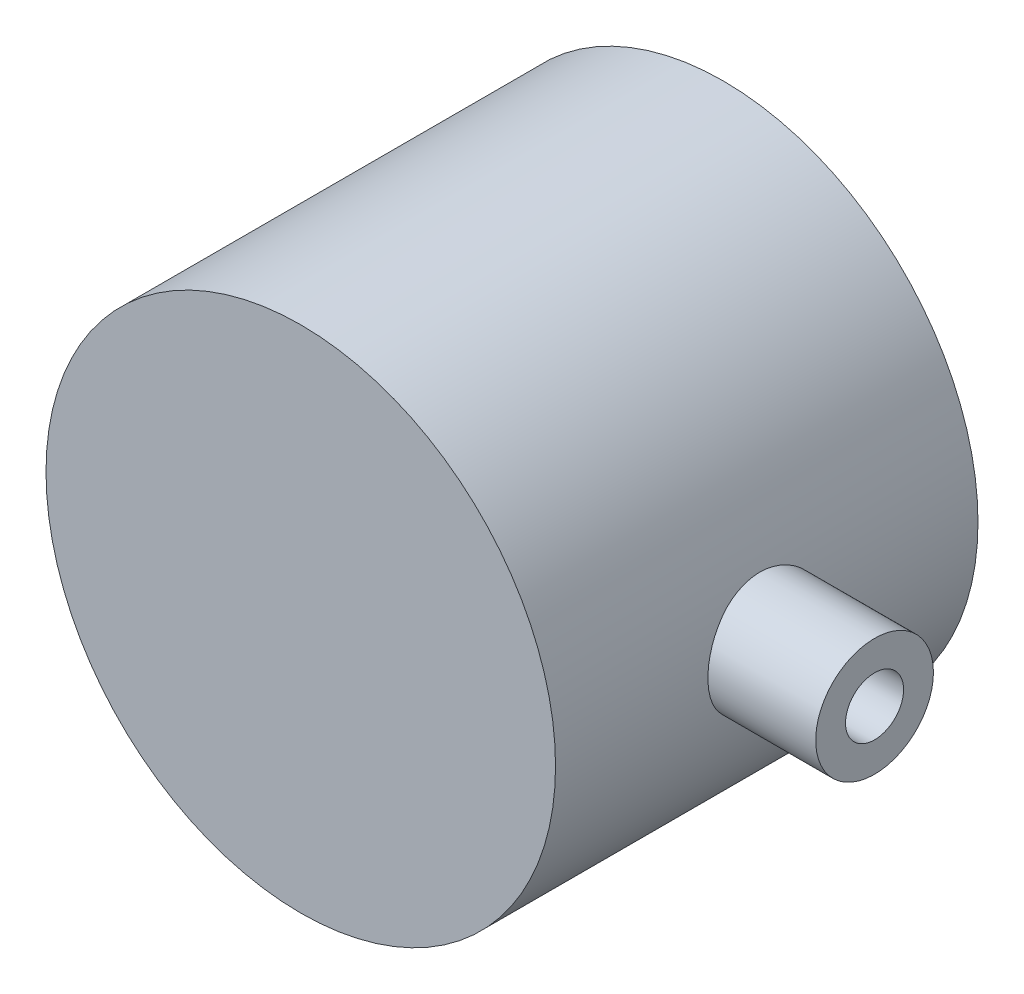
SolidWorks part; units mm, degrees
ref_plane "Ebene vorne" through (0, 0, 0) normal (0, 0, 1) x (1, 0, 0)
ref_plane "Ebene oben" through (0, 0, 0) normal (0, 1, 0) x (1, 0, 0)
ref_plane "Ebene rechts" through (0, 0, 0) normal (1, 0, 0) x (0, 0, -1)
sketch "Sketch1" plane through (0, 0, 0) normal (0, 0, 1) x (1, 0, 0)
  circle A1 centre (0, 0) radius 24.123
  dimension "D3" = 48.246
extrude "Boss-Extrude1" add sketch "Sketch1" along normal blind 35 and the other way blind 5
sketch "Sketch2" plane through (0, 0, 0) normal (1, 0, 0) x (0, 0, -1)
  line L0 (0, 24.123) -> (0, -24.123) construction
  circle A0 centre (-15, 0) radius 3.25
  dimension "D1" = 15
  dimension "D2" = 6.5
extrude "Cut-Extrude2" cut sketch "Sketch2" along normal blind 19.25
sketch "Sketch4" plane through (0, 0, 0) normal (0, 1, 0) x (1, 0, 0)
  line L0 (0, -18.25) -> (0, -11.75) construction
  line L1 (-24.123, 0) -> (24.123, 0) construction
  circle A0 centre (0, -15) radius 2.75
  dimension "D1" = 15
  dimension "D2" = 5.5
extrude "Cut-Extrude3" cut sketch "Sketch4" against normal blind 200
sketch "Sketch6" plane through (0, 0, 0) normal (0, 1, 0) x (1, 0, 0)
  line L0 (0, -18.25) -> (0, -11.75) construction
  line L1 (-24.123, -35) -> (24.123, -35) construction
  circle A0 centre (0, -15) radius 5.25
  dimension "D1" = 20
  dimension "D2" = 10.5
extrude "Cut-Extrude9" cut sketch "Sketch6" along normal blind 4.533 from offset 24.123 offset against normal yes
sketch "Sketch7" plane through (0, 0, -5) normal (0, 0, -1) x (-1, 0, 0)
  circle A0 centre (0, 0) radius 17.25
  dimension "D1" = 34.5
extrude "Cut-Extrude10" cut sketch "Sketch7" against normal blind 30
sketch "Sketch8" plane through (0, 0, 0) normal (1, 0, 0) x (0, 0, -1)
  circle A0 centre (-15, 0) radius 2.75
  dimension "D1" = 5.5
extrude "Cut-Extrude11" cut sketch "Sketch8" along normal blind 24.873 from offset 19.25
sketch "Sketch9" plane through (0, 0, 0) normal (1, 0, 0) x (0, 0, -1)
  circle A0 centre (-15, 0) radius 5.575
extrude "Boss-Extrude2" add sketch "Sketch9" along normal blind 11.203 from offset 23.125 separate body
extrude "Cut-Extrude12" cut sketch "Sketch8" along normal blind 50
sketch "Sketch12" plane through (0, 0, 0) normal (0, 1, 0) x (1, 0, 0)
  circle A0 centre (0, -15) radius 8.25
  dimension "D1" = 16.5
extrude "Cut-Extrude14" cut sketch "Sketch12" along normal blind 2 from offset 24.125 offset against normal yes
sketch "Sketch13" plane through (0, 0, 0) normal (0, 1, 0) x (1, 0, 0)
  circle A0 centre (0, -15) radius 3.25
  dimension "D1" = 6.5
extrude "Cut-Extrude15" cut sketch "Sketch13" against normal blind 19.09
pattern_circular "CirPattern1" count 2 over 45 about axis through (0, 0, 25) along (0, 0, -1) of "Cut-Extrude9", "Cut-Extrude3", "Cut-Extrude14", "Cut-Extrude15"
